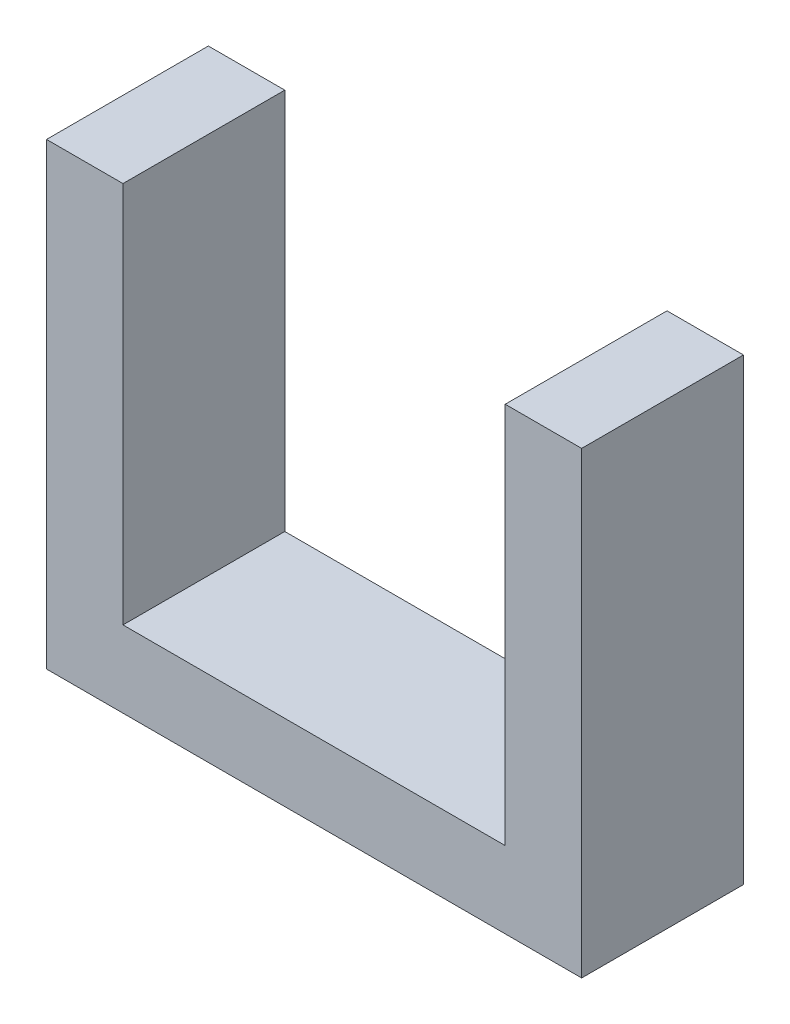
SolidWorks part; units mm, degrees
ref_plane "Front Plane" through (0, 0, 0) normal (0, 0, 1) x (1, 0, 0)
ref_plane "Top Plane" through (0, 0, 0) normal (0, 1, 0) x (1, 0, 0)
ref_plane "Right Plane" through (0, 0, 0) normal (1, 0, 0) x (0, 0, -1)
sketch "Sketch1" plane through (0, 0, 0) normal (0, 0, 1) x (1, 0, 0)
  line L0 (-18.2824, 18.4603) -> (-18.2824, 3.4603)
  line L1 (-18.2824, 3.4603) -> (-3.2824, 3.4603)
  line L2 (-3.2824, 3.4603) -> (-3.2824, 18.4603)
  line L3 (-3.2824, 18.4603) -> (-0.2824, 18.4603)
  line L4 (-0.2824, 18.4603) -> (-0.2824, 0.4603)
  line L5 (-0.2824, 0.4603) -> (-21.2824, 0.4603)
  line L6 (-21.2824, 0.4603) -> (-21.2824, 18.4603)
  line L7 (-21.2824, 18.4603) -> (-18.2824, 18.4603)
extrude "Boss-Extrude1" add sketch "Sketch1" along normal blind 6.35
